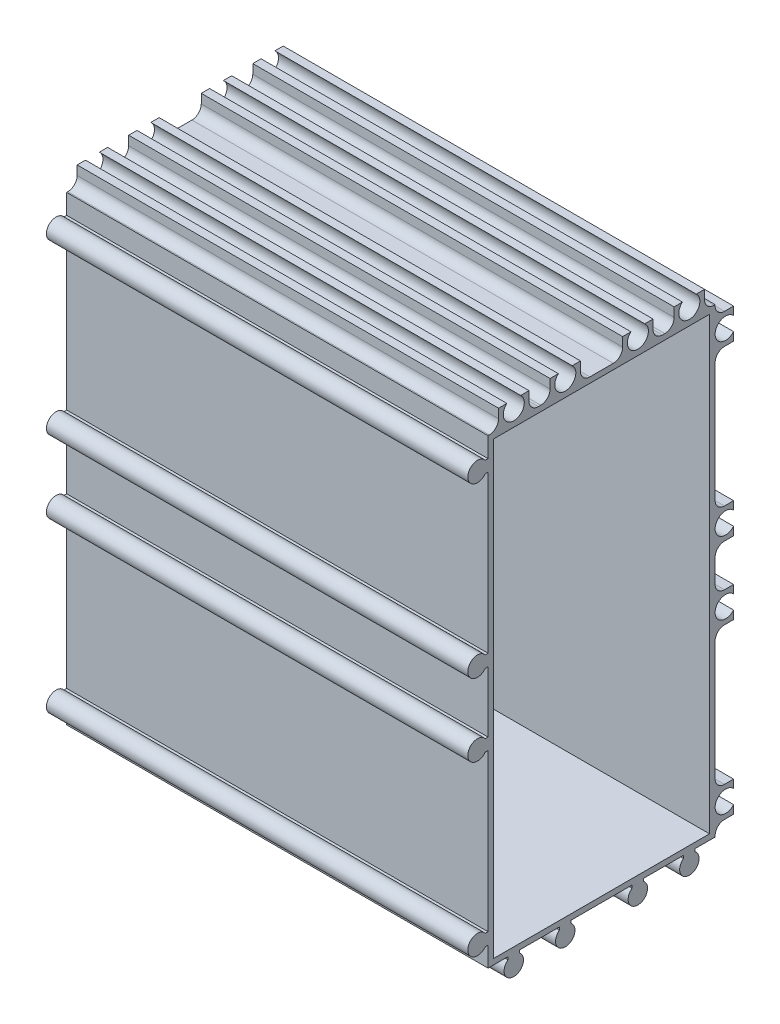
SolidWorks part; units mm, degrees
ref_plane "Спереди" through (0, 0, 0) normal (0, 0, 1) x (1, 0, 0)
ref_plane "Сверху" through (0, 0, 0) normal (0, 1, 0) x (1, 0, 0)
ref_plane "Справа" through (0, 0, 0) normal (1, 0, 0) x (0, 0, -1)
ref_plane "Плоскость4" through (90, 0, 0) normal (1, 0, 0) x (0, 0, -1)
sketch "Эскиз1" plane through (90, 0, 0) normal (1, 0, 0) x (0, 0, -1)
  line L0 (6.75, 225.9062) -> (6.75, 320.75)
  line L1 (6.75, 320.75) -> (-38.0938, 320.75)
  line L2 (-38.0938, 318.25) -> (-37.5, 318.25)
  line L3 (-37.5, 318.25) -> (-37.5, 284.75)
  line L4 (-37.5, 284.75) -> (-38.0938, 284.75)
  line L5 (-38.0938, 282.25) -> (-37.5, 282.25)
  line L6 (-37.5, 282.25) -> (-37.5, 269.25)
  line L7 (-37.5, 269.25) -> (-38.0938, 269.25)
  line L8 (-38.0938, 266.75) -> (-37.5, 266.75)
  line L9 (-37.5, 266.75) -> (-37.5, 233.25)
  line L10 (-37.5, 233.25) -> (-38.0938, 233.25)
  line L11 (-38.0938, 230.75) -> (-37.5, 230.75)
  line L12 (-37.5, 230.75) -> (-37.5, 226.5)
  line L13 (-37.5, 226.5) -> (-33.25, 226.5)
  line L14 (-33.25, 226.5) -> (-33.25, 225.9062)
  line L15 (-30.75, 225.9062) -> (-30.75, 226.5)
  line L16 (-30.75, 226.5) -> (-22.25, 226.5)
  line L17 (-22.25, 226.5) -> (-22.25, 225.9062)
  line L18 (-19.75, 225.9062) -> (-19.75, 226.5)
  line L19 (-19.75, 226.5) -> (-6.75, 226.5)
  line L20 (-6.75, 226.5) -> (-6.75, 225.9062)
  line L21 (-4.25, 225.9062) -> (-4.25, 226.5)
  line L22 (-4.25, 226.5) -> (4.25, 226.5)
  line L23 (4.25, 226.5) -> (4.25, 225.9062)
  arc A0 (-38.0938, 320.75) -> (-38.0938, 318.25) centre (-39.75, 319.5) ccw
  arc A1 (-38.0938, 284.75) -> (-38.0938, 282.25) centre (-39.75, 283.5) ccw
  arc A2 (-38.0938, 269.25) -> (-38.0938, 266.75) centre (-39.75, 268) ccw
  arc A3 (-38.0938, 233.25) -> (-38.0938, 230.75) centre (-39.75, 232) ccw
  arc A4 (-33.25, 225.9062) -> (-30.75, 225.9062) centre (-32, 224.25) ccw
  arc A5 (-22.25, 225.9062) -> (-19.75, 225.9062) centre (-21, 224.25) ccw
  arc A6 (-6.75, 225.9062) -> (-4.25, 225.9062) centre (-5.5, 224.25) ccw
  arc A7 (4.25, 225.9062) -> (6.75, 225.9062) centre (5.5, 224.25) ccw
extrude "Бобышка-Вытянуть1" add sketch "Эскиз1" against normal blind 90
sketch "Эскиз2" plane through (0, 320.75, 0) normal (0, 1, 0) x (-1, 0, 0)
  line L0 (-90, -6.75) -> (-90, 37.5)
  line L1 (-90, 37.5) -> (0, 37.5)
  line L2 (0, 37.5) -> (0, -6.75)
  line L3 (0, -6.75) -> (-90, -6.75)
extrude "Бобышка-Вытянуть2" add sketch "Эскиз2" along normal blind 8.2
sketch "Эскиз3" plane through (0, 0, -6.75) normal (0, 0, -1) x (-1, 0, 0)
  line L0 (-90, 226.5) -> (-90, 328.95)
  line L1 (-90, 328.95) -> (0, 328.95)
  line L2 (0, 328.95) -> (0, 226.5)
  line L3 (0, 226.5) -> (-90, 226.5)
extrude "Бобышка-Вытянуть3" add sketch "Эскиз3" along normal blind 8.2
sketch "Эскиз4" plane through (0, 0, 0) normal (-1, 0, 0) x (0, 0, 1)
  line L0 (24.25, 328.95) -> (24.25, 325)
  line L1 (24.25, 325) -> (28.75, 325)
  line L2 (28.75, 325) -> (28.75, 328.95)
  line L3 (28.75, 328.95) -> (24.25, 328.95)
extrude "Вырез-Вытянуть1" cut sketch "Эскиз4" against normal through all
sketch "Эскиз5" plane through (0, 0, 0) normal (-1, 0, 0) x (0, 0, 1)
  line L0 (37.5, 328.95) -> (35.25, 328.95)
  line L1 (35.25, 328.95) -> (35.25, 325)
  line L2 (35.25, 325) -> (37.5, 325)
  line L3 (37.5, 325) -> (37.5, 328.95)
extrude "Вырез-Вытянуть2" cut sketch "Эскиз5" against normal through all
sketch "Эскиз6" plane through (0, 0, 0) normal (-1, 0, 0) x (0, 0, 1)
  line L0 (-14.95, 226.5) -> (-11, 226.5)
  line L1 (-11, 226.5) -> (-11, 228.75)
  line L2 (-11, 228.75) -> (-14.95, 228.75)
  line L3 (-14.95, 228.75) -> (-14.95, 226.5)
extrude "Вырез-Вытянуть3" cut sketch "Эскиз6" against normal through all
sketch "Эскиз7" plane through (0, 0, 0) normal (-1, 0, 0) x (0, 0, 1)
  line L0 (-14.95, 235.25) -> (-11, 235.25)
  line L1 (-11, 235.25) -> (-11, 264.75)
  line L2 (-11, 264.75) -> (-14.95, 264.75)
  line L3 (-14.95, 264.75) -> (-14.95, 235.25)
extrude "Вырез-Вытянуть4" cut sketch "Эскиз7" against normal through all
sketch "Эскиз8" plane through (0, 0, 0) normal (-1, 0, 0) x (0, 0, 1)
  line L0 (-14.95, 271.25) -> (-11, 271.25)
  line L1 (-11, 271.25) -> (-11, 280.25)
  line L2 (-11, 280.25) -> (-14.95, 280.25)
  line L3 (-14.95, 280.25) -> (-14.95, 271.25)
extrude "Вырез-Вытянуть5" cut sketch "Эскиз8" against normal through all
sketch "Эскиз9" plane through (0, 0, 0) normal (-1, 0, 0) x (0, 0, 1)
  line L0 (-14.95, 286.75) -> (-11, 286.75)
  line L1 (-11, 286.75) -> (-11, 316.25)
  line L2 (-11, 316.25) -> (-14.95, 316.25)
  line L3 (-14.95, 316.25) -> (-14.95, 286.75)
extrude "Вырез-Вытянуть6" cut sketch "Эскиз9" against normal through all
sketch "Эскиз10" plane through (0, 0, 0) normal (-1, 0, 0) x (0, 0, 1)
  line L0 (-14.95, 328.95) -> (-14.95, 322.75)
  line L1 (-14.95, 322.75) -> (-11, 322.75)
  line L2 (-11, 322.75) -> (-11, 328.95)
  line L3 (-11, 328.95) -> (-14.95, 328.95)
extrude "Вырез-Вытянуть7" cut sketch "Эскиз10" against normal through all
sketch "Эскиз11" plane through (0, 0, 0) normal (-1, 0, 0) x (0, 0, 1)
  line L0 (-11, 328.95) -> (-11, 325)
  line L1 (-11, 325) -> (-8.75, 325)
  line L2 (-8.75, 325) -> (-8.75, 328.95)
  line L3 (-8.75, 328.95) -> (-11, 328.95)
extrude "Вырез-Вытянуть8" cut sketch "Эскиз11" against normal through all
sketch "Эскиз12" plane through (0, 0, 0) normal (-1, 0, 0) x (0, 0, 1)
  line L0 (-2.25, 328.95) -> (-2.25, 325)
  line L1 (-2.25, 325) -> (2.25, 325)
  line L2 (2.25, 325) -> (2.25, 328.95)
  line L3 (2.25, 328.95) -> (-2.25, 328.95)
extrude "Вырез-Вытянуть9" cut sketch "Эскиз12" against normal through all
sketch "Эскиз13" plane through (0, 0, 0) normal (-1, 0, 0) x (0, 0, 1)
  line L0 (8.75, 328.95) -> (8.75, 325)
  line L1 (8.75, 325) -> (17.75, 325)
  line L2 (17.75, 325) -> (17.75, 328.95)
  line L3 (17.75, 328.95) -> (8.75, 328.95)
extrude "Вырез-Вытянуть10" cut sketch "Эскиз13" against normal through all
sketch "Эскиз14" plane through (90, 0, 0) normal (1, 0, 0) x (0, 0, -1)
  line L0 (9.8, 323.8) -> (-36.3, 323.8)
  line L1 (-36.3, 323.8) -> (-36.3, 227.7)
  line L2 (-36.3, 227.7) -> (9.8, 227.7)
  line L3 (9.8, 227.7) -> (9.8, 323.8)
  line L4 (-37.5, 318.25) -> (-37.5, 284.75) construction
  line L5 (-8.75, 325) -> (-17.75, 325) construction
  line L6 (11, 286.75) -> (11, 316.25) construction
  line L7 (-19.75, 226.5) -> (-6.75, 226.5) construction
  dimension "D1" = 1.2
  dimension "D2" = 1.2
  dimension "D3" = 1.2
  dimension "D4" = 1.2
extrude "Вырез-Вытянуть11" cut sketch "Эскиз14" against normal blind 86.6
hole_wizard "Диаметр отверстия Ø2.5 (2.5)1" positions "Эскиз16" profile "Эскиз15" hole size "Ø2.5" standard "Ansi Metric"
sketch "Эскиз16" plane through (90, 0, 0) normal (1, 0, 0) x (0, 0, -1)
  point P0 (-39.75, 232)
  point P1 (-21, 224.25)
  point P2 (-39.75, 283.5)
  point P3 (-5.5, 224.25)
  point P4 (5.5, 224.25)
  point P5 (-39.75, 319.5)
  point P6 (-39.75, 268)
  point P7 (-32, 224.25)
sketch "Эскиз15" plane through (90, 232, 39.75) normal (0, 1, 0) x (0, 0, -1)
  line L0 (0, 0) -> (0, 90)
  line L1 (0, 90) -> (1.25, 90)
  line L2 (1.25, 90) -> (1.25, 0)
  line L5 (1.25, 0) -> (0, 0)
  line L11 (0, -6.35) -> (0, 107.95) construction
  dimension "Диаметр сквозного отверстия" = 2.5
  dimension "Глубина сквозного отверстия" = 90
hole_wizard "Диаметр отверстия Ø4.5 (4.5)1" positions "Эскиз18" profile "Эскиз17" hole size "Ø4.5" standard "Ansi Metric"
sketch "Эскиз18" plane through (0, 0, 0) normal (-1, 0, 0) x (0, 0, 1)
  point P0 (21, 327.25)
  point P1 (32, 327.25)
  point P2 (-13.25, 232)
  point P3 (-13.25, 268)
  point P4 (-13.25, 283.5)
  point P5 (-13.25, 319.5)
  point P6 (-5.5, 327.25)
  point P7 (5.5, 327.25)
sketch "Эскиз17" plane through (0, 327.25, 21) normal (0, 1, 0) x (0, 0, 1)
  line L0 (0, 0) -> (0, 90)
  line L1 (0, 90) -> (2.25, 90)
  line L2 (2.25, 90) -> (2.25, 0)
  line L5 (2.25, 0) -> (0, 0)
  line L11 (0, -6.35) -> (0, 107.95) construction
  dimension "Диаметр сквозного отверстия" = 4.5
  dimension "Глубина сквозного отверстия" = 90
hole_wizard "Диаметр отверстия Ø8.3 (8.3)1" [suppressed] positions "Эскиз20" profile "Эскиз19" hole size "Ø8.3" standard "Ansi Metric"
sketch "Эскиз20" plane through (0, 0, 0) normal (-1, 0, 0) x (0, 0, 1)
  point P0 (13.25, 275.75)
sketch "Эскиз19" plane through (0, 275.75, 13.25) normal (0, 1, 0) x (0, 0, 1)
  line L0 (0, 0) -> (0, 3.2)
  line L1 (0, 3.2) -> (4.15, 3.2)
  line L2 (4.15, 3.2) -> (4.15, 0)
  line L5 (4.15, 0) -> (0, 0)
  line L10 (0, 3.2) -> (-4.15, 3.2) construction
  line L11 (0, -6.35) -> (0, 107.95) construction
  dimension "Диаметр отверстия" = 8.3
  dimension "Глубина отверстия" = 3.2
  dimension "Угол заточки сверла" = 180
sketch "Эскиз21" [suppressed] plane through (0, 0, 0) normal (-1, 0, 0) x (0, 0, 1)
  circle A0 centre (13.25, 275.75) radius 4.15
extrude "Вырез-Вытянуть12" [suppressed] cut sketch "Эскиз21" against normal blind 10
sketch "Эскиз22" plane through (90, 0, 0) normal (1, 0, 0) x (0, 0, -1)
  circle A0 centre (-39.75, 319.5) radius 1.6316
  circle A1 centre (-39.75, 283.5) radius 1.5194
  circle A2 centre (-39.75, 268) radius 1.4876
  circle A3 centre (-39.75, 232) radius 1.5817
  circle A4 centre (-32, 224.25) radius 1.4878
  circle A5 centre (-21, 224.25) radius 1.426
  circle A6 centre (-5.5, 224.25) radius 1.6281
  circle A7 centre (5.5, 224.25) radius 1.5237
extrude "Бобышка-Вытянуть4" add sketch "Эскиз22" against normal blind 90
fillet "Скругление1" [suppressed] radius 2
fillet "Скругление2" [suppressed] radius 2
fillet "Скругление3" [suppressed] radius 2
fillet "Скругление4" [suppressed] radius 2
fillet "Скругление5" radius 2 1 edges at (45, 325, 35.25)
fillet "Скругление6" radius 2 1 edges at (45, 325, 28.75)
fillet "Скругление7" radius 2 1 edges at (45, 325, 24.25)
fillet "Скругление8" radius 2 1 edges at (45, 325, 17.75)
fillet "Скругление9" radius 2 1 edges at (45, 325, 8.75)
fillet "Скругление10" radius 2 1 edges at (45, 325, 2.25)
fillet "Скругление11" radius 2 1 edges at (45, 325, -2.25)
fillet "Скругление12" radius 2 1 edges at (45, 325, -8.75)
fillet "Скругление13" radius 2 1 edges at (45, 322.75, -11)
fillet "Скругление14" radius 2 1 edges at (45, 316.25, -11)
fillet "Скругление15" radius 2 1 edges at (45, 286.75, -11)
fillet "Скругление16" radius 2 1 edges at (45, 280.25, -11)
fillet "Скругление17" radius 2 1 edges at (45, 271.25, -11)
fillet "Скругление18" radius 2 1 edges at (45, 264.75, -11)
fillet "Скругление19" radius 2 1 edges at (45, 235.25, -11)
fillet "Скругление20" radius 2 1 edges at (45, 228.75, -11)
equation "\"D2@Эскиз14\"=\"D1@Эскиз14\""
equation "\"D3@Эскиз14\"=\"D1@Эскиз14\""
equation "\"D4@Эскиз14\"=\"D1@Эскиз14\""
